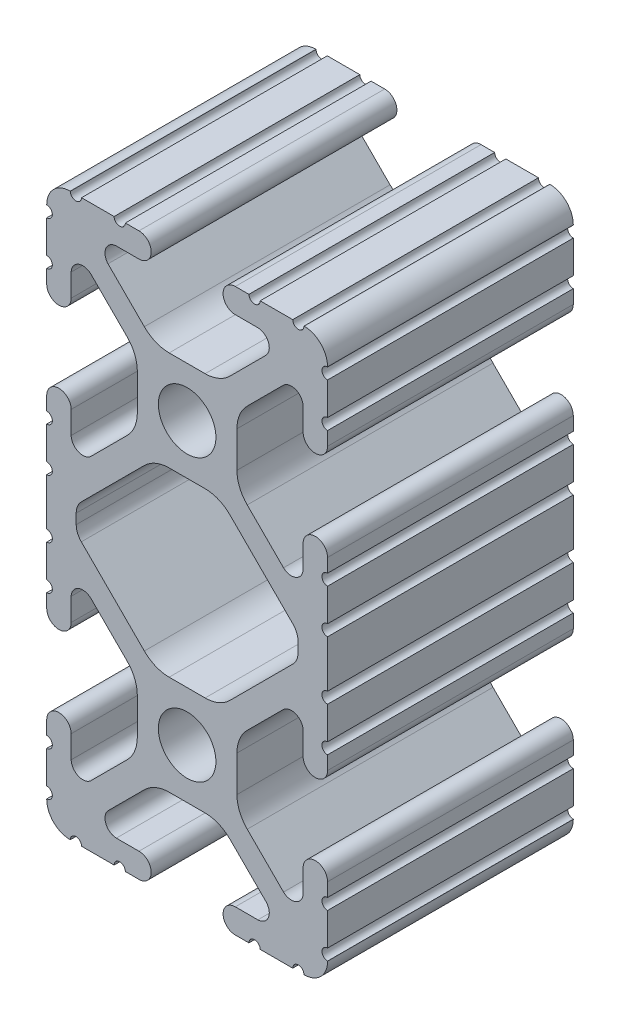
SolidWorks part; units mm, degrees
ref_plane "Front Plane" through (0, 0, 0) normal (0, 0, 1) x (1, 0, 0)
ref_plane "Top Plane" through (0, 0, 0) normal (0, 1, 0) x (1, 0, 0)
ref_plane "Right Plane" through (0, 0, 0) normal (1, 0, 0) x (0, 0, -1)
sketch "Sketch1" plane through (0, 0, 0) normal (0, 0, 1) x (1, 0, 0)
  line L0 (902.297, 599.2494) -> (902.297, 600.1524)
  line L1 (902.7583, 601.2659) -> (908.4588, 606.9666)
  line L2 (910.7039, 607.8966) -> (913.9563, 607.8966)
  line L3 (916.2014, 606.9666) -> (921.9018, 601.266)
  line L4 (922.363, 600.1525) -> (922.363, 599.2495)
  line L5 (921.9018, 598.136) -> (916.2013, 592.4353)
  line L6 (913.9562, 591.5053) -> (910.7038, 591.5053)
  line L7 (908.4587, 592.4353) -> (902.7583, 598.1358)
  line L8 (925.03, 602.8505) -> (925.03, 605.7969)
  line L9 (925.03, 606.8129) -> (925.03, 608.0448)
  line L10 (922.8202, 608.0448) -> (922.8202, 605.996)
  line L11 (921.0484, 605.2457) -> (917.7644, 608.5297)
  line L12 (916.8344, 610.7748) -> (916.8344, 614.0272)
  line L13 (917.7644, 616.2723) -> (921.0482, 619.556)
  line L14 (922.8202, 618.7995) -> (922.8202, 616.757)
  line L15 (925.03, 616.757) -> (925.03, 617.9889)
  line L16 (925.03, 619.0049) -> (925.03, 621.9513)
  line L17 (925.03, 622.9673) -> (925.03, 622.9927)
  line L18 (922.9218, 625.1009) -> (922.8964, 625.1009)
  line L19 (921.8804, 625.1009) -> (918.934, 625.1009)
  line L20 (917.918, 625.1009) -> (916.6861, 625.1009)
  line L21 (916.6861, 622.8911) -> (918.735, 622.8911)
  line L22 (919.4852, 621.1193) -> (916.2013, 617.8353)
  line L23 (913.9562, 616.9053) -> (910.7038, 616.9053)
  line L24 (908.4587, 617.8353) -> (905.175, 621.1191)
  line L25 (905.9315, 622.8911) -> (907.9739, 622.8911)
  line L26 (907.9739, 625.1009) -> (906.742, 625.1009)
  line L27 (905.726, 625.1009) -> (902.7796, 625.1009)
  line L28 (901.7636, 625.1009) -> (901.7382, 625.1009)
  line L29 (899.63, 622.9927) -> (899.63, 622.9673)
  line L30 (899.63, 621.9513) -> (899.63, 619.0049)
  line L31 (899.63, 617.9889) -> (899.63, 616.757)
  line L32 (901.8398, 616.757) -> (901.8398, 618.8059)
  line L33 (903.6117, 619.5561) -> (906.8957, 616.2722)
  line L34 (907.8257, 614.0271) -> (907.8257, 610.7747)
  line L35 (906.8957, 608.5296) -> (903.6119, 605.2459)
  line L36 (901.8398, 606.0024) -> (901.8398, 608.0448)
  line L37 (899.63, 608.0448) -> (899.63, 606.8129)
  line L38 (899.63, 605.7969) -> (899.63, 602.8505)
  line L39 (899.63, 601.8345) -> (899.63, 597.5673)
  line L40 (899.63, 596.5513) -> (899.63, 593.6049)
  line L41 (899.63, 592.5889) -> (899.63, 591.357)
  line L42 (901.8398, 591.357) -> (901.8398, 593.4059)
  line L43 (903.6117, 594.1561) -> (906.8957, 590.8722)
  line L44 (907.8257, 588.6271) -> (907.8257, 585.3747)
  line L45 (906.8957, 583.1296) -> (903.6119, 579.8459)
  line L46 (901.8398, 580.6024) -> (901.8398, 582.6448)
  line L47 (899.63, 582.6448) -> (899.63, 581.4129)
  line L48 (899.63, 580.3969) -> (899.63, 577.4505)
  line L49 (899.63, 576.4345) -> (899.63, 576.4091)
  line L50 (901.7382, 574.3009) -> (901.7636, 574.3009)
  line L51 (902.7796, 574.3009) -> (905.726, 574.3009)
  line L52 (906.742, 574.3009) -> (907.9739, 574.3009)
  line L53 (907.9739, 576.5107) -> (905.9251, 576.5107)
  line L54 (905.1749, 578.2826) -> (908.4588, 581.5666)
  line L55 (910.7039, 582.4966) -> (913.9563, 582.4966)
  line L56 (916.2014, 581.5666) -> (919.4851, 578.2828)
  line L57 (918.7286, 576.5107) -> (916.6861, 576.5107)
  line L58 (916.6861, 574.3009) -> (917.918, 574.3009)
  line L59 (918.934, 574.3009) -> (921.8804, 574.3009)
  line L60 (922.8964, 574.3009) -> (922.9218, 574.3009)
  line L61 (925.03, 576.4091) -> (925.03, 576.4345)
  line L62 (925.03, 577.4505) -> (925.03, 580.3969)
  line L63 (925.03, 581.4129) -> (925.03, 582.6448)
  line L64 (922.8202, 582.6448) -> (922.8202, 580.596)
  line L65 (921.0484, 579.8457) -> (917.7644, 583.1297)
  line L66 (916.8344, 585.3748) -> (916.8344, 588.6272)
  line L67 (917.7644, 590.8723) -> (921.0482, 594.156)
  line L68 (922.8202, 593.3995) -> (922.8202, 591.357)
  line L69 (925.03, 591.357) -> (925.03, 592.5889)
  line L70 (925.03, 593.6049) -> (925.03, 596.5513)
  line L71 (925.03, 597.5673) -> (925.03, 601.8345)
  arc A0 (902.7583, 601.2659) -> (902.297, 600.1524) centre (903.8718, 600.1524) ccw
  arc A1 (910.7039, 607.8966) -> (908.4588, 606.9666) centre (910.7039, 604.7216) ccw
  arc A2 (916.2014, 606.9666) -> (913.9563, 607.8966) centre (913.9563, 604.7216) ccw
  arc A3 (922.363, 600.1525) -> (921.9018, 601.266) centre (920.7882, 600.1525) ccw
  arc A4 (921.9018, 598.136) -> (922.363, 599.2495) centre (920.7882, 599.2495) ccw
  arc A5 (913.9562, 591.5053) -> (916.2013, 592.4353) centre (913.9562, 594.6803) ccw
  arc A6 (908.4587, 592.4353) -> (910.7038, 591.5053) centre (910.7038, 594.6803) ccw
  arc A7 (902.297, 599.2494) -> (902.7583, 598.1358) centre (903.8718, 599.2494) ccw
  circle A8 centre (912.33, 612.4009) radius 2.6035
  circle A9 centre (912.33, 587.0009) radius 2.6035
  arc A10 (925.03, 602.8505) -> (925.03, 601.8345) centre (925.03, 602.3425) ccw
  arc A11 (925.03, 606.8129) -> (925.03, 605.7969) centre (925.03, 606.3049) ccw
  arc A12 (925.03, 608.0448) -> (922.8202, 608.0448) centre (923.9251, 608.0448) ccw
  arc A13 (921.0484, 605.2457) -> (922.8202, 605.996) centre (921.7603, 606.0319) ccw
  arc A14 (916.8344, 610.7748) -> (917.7644, 608.5297) centre (920.0094, 610.7748) ccw
  arc A15 (917.7644, 616.2723) -> (916.8344, 614.0272) centre (920.0094, 614.0272) ccw
  arc A16 (922.8202, 618.7995) -> (921.0482, 619.556) centre (921.7601, 618.7699) ccw
  arc A17 (922.8202, 616.757) -> (925.03, 616.757) centre (923.9251, 616.757) ccw
  arc A18 (925.03, 619.0049) -> (925.03, 617.9889) centre (925.03, 618.4969) ccw
  arc A19 (925.03, 622.9673) -> (925.03, 621.9513) centre (925.03, 622.4593) ccw
  arc A20 (925.03, 622.9927) -> (922.9218, 625.1009) centre (922.9218, 622.9927) ccw
  arc A21 (921.8804, 625.1009) -> (922.8964, 625.1009) centre (922.3884, 625.1009) ccw
  arc A22 (917.918, 625.1009) -> (918.934, 625.1009) centre (918.426, 625.1009) ccw
  arc A23 (916.6861, 625.1009) -> (916.6861, 622.8911) centre (916.6861, 623.996) ccw
  arc A24 (919.4852, 621.1193) -> (918.735, 622.8911) centre (918.6991, 621.8312) ccw
  arc A25 (913.9562, 616.9053) -> (916.2013, 617.8353) centre (913.9562, 620.0803) ccw
  arc A26 (908.4587, 617.8353) -> (910.7038, 616.9053) centre (910.7038, 620.0803) ccw
  arc A27 (905.9315, 622.8911) -> (905.175, 621.1191) centre (905.9611, 621.831) ccw
  arc A28 (907.9739, 622.8911) -> (907.9739, 625.1009) centre (907.9739, 623.996) ccw
  arc A29 (905.726, 625.1009) -> (906.742, 625.1009) centre (906.234, 625.1009) ccw
  arc A30 (901.7636, 625.1009) -> (902.7796, 625.1009) centre (902.2716, 625.1009) ccw
  arc A31 (901.7382, 625.1009) -> (899.63, 622.9927) centre (901.7382, 622.9927) ccw
  arc A32 (899.63, 621.9513) -> (899.63, 622.9673) centre (899.63, 622.4593) ccw
  arc A33 (899.63, 617.9889) -> (899.63, 619.0049) centre (899.63, 618.4969) ccw
  arc A34 (899.63, 616.757) -> (901.8398, 616.757) centre (900.7349, 616.757) ccw
  arc A35 (903.6117, 619.5561) -> (901.8398, 618.8059) centre (902.8998, 618.77) ccw
  arc A36 (907.8257, 614.0271) -> (906.8957, 616.2722) centre (904.6507, 614.0271) ccw
  arc A37 (906.8957, 608.5296) -> (907.8257, 610.7747) centre (904.6507, 610.7747) ccw
  arc A38 (901.8398, 606.0024) -> (903.6119, 605.2459) centre (902.9, 606.032) ccw
  arc A39 (901.8398, 608.0448) -> (899.63, 608.0448) centre (900.7349, 608.0448) ccw
  arc A40 (899.63, 605.7969) -> (899.63, 606.8129) centre (899.63, 606.3049) ccw
  arc A41 (899.63, 601.8345) -> (899.63, 602.8505) centre (899.63, 602.3425) ccw
  arc A42 (899.63, 596.5513) -> (899.63, 597.5673) centre (899.63, 597.0593) ccw
  arc A43 (899.63, 592.5889) -> (899.63, 593.6049) centre (899.63, 593.0969) ccw
  arc A44 (899.63, 591.357) -> (901.8398, 591.357) centre (900.7349, 591.357) ccw
  arc A45 (903.6117, 594.1561) -> (901.8398, 593.4059) centre (902.8998, 593.37) ccw
  arc A46 (907.8257, 588.6271) -> (906.8957, 590.8722) centre (904.6507, 588.6271) ccw
  arc A47 (906.8957, 583.1296) -> (907.8257, 585.3747) centre (904.6507, 585.3747) ccw
  arc A48 (901.8398, 580.6024) -> (903.6119, 579.8459) centre (902.9, 580.632) ccw
  arc A49 (901.8398, 582.6448) -> (899.63, 582.6448) centre (900.7349, 582.6448) ccw
  arc A50 (899.63, 580.3969) -> (899.63, 581.4129) centre (899.63, 580.9049) ccw
  arc A51 (899.63, 576.4345) -> (899.63, 577.4505) centre (899.63, 576.9425) ccw
  arc A52 (899.63, 576.4091) -> (901.7382, 574.3009) centre (901.7382, 576.4091) ccw
  arc A53 (902.7796, 574.3009) -> (901.7636, 574.3009) centre (902.2716, 574.3009) ccw
  arc A54 (906.742, 574.3009) -> (905.726, 574.3009) centre (906.234, 574.3009) ccw
  arc A55 (907.9739, 574.3009) -> (907.9739, 576.5107) centre (907.9739, 575.4058) ccw
  arc A56 (905.1749, 578.2826) -> (905.9251, 576.5107) centre (905.961, 577.5707) ccw
  arc A57 (910.7039, 582.4966) -> (908.4588, 581.5666) centre (910.7039, 579.3216) ccw
  arc A58 (916.2014, 581.5666) -> (913.9563, 582.4966) centre (913.9563, 579.3216) ccw
  arc A59 (918.7286, 576.5107) -> (919.4851, 578.2828) centre (918.699, 577.5709) ccw
  arc A60 (916.6861, 576.5107) -> (916.6861, 574.3009) centre (916.6861, 575.4058) ccw
  arc A61 (918.934, 574.3009) -> (917.918, 574.3009) centre (918.426, 574.3009) ccw
  arc A62 (922.8964, 574.3009) -> (921.8804, 574.3009) centre (922.3884, 574.3009) ccw
  arc A63 (922.9218, 574.3009) -> (925.03, 576.4091) centre (922.9218, 576.4091) ccw
  arc A64 (925.03, 577.4505) -> (925.03, 576.4345) centre (925.03, 576.9425) ccw
  arc A65 (925.03, 581.4129) -> (925.03, 580.3969) centre (925.03, 580.9049) ccw
  arc A66 (925.03, 582.6448) -> (922.8202, 582.6448) centre (923.9251, 582.6448) ccw
  arc A67 (921.0484, 579.8457) -> (922.8202, 580.596) centre (921.7603, 580.6319) ccw
  arc A68 (916.8344, 585.3748) -> (917.7644, 583.1297) centre (920.0094, 585.3748) ccw
  arc A69 (917.7644, 590.8723) -> (916.8344, 588.6272) centre (920.0094, 588.6272) ccw
  arc A70 (922.8202, 593.3995) -> (921.0482, 594.156) centre (921.7601, 593.3699) ccw
  arc A71 (922.8202, 591.357) -> (925.03, 591.357) centre (923.9251, 591.357) ccw
  arc A72 (925.03, 593.6049) -> (925.03, 592.5889) centre (925.03, 593.0969) ccw
  arc A73 (925.03, 597.5673) -> (925.03, 596.5513) centre (925.03, 597.0593) ccw
extrude "Extrude1" add sketch "Sketch1" against normal blind 22.225
